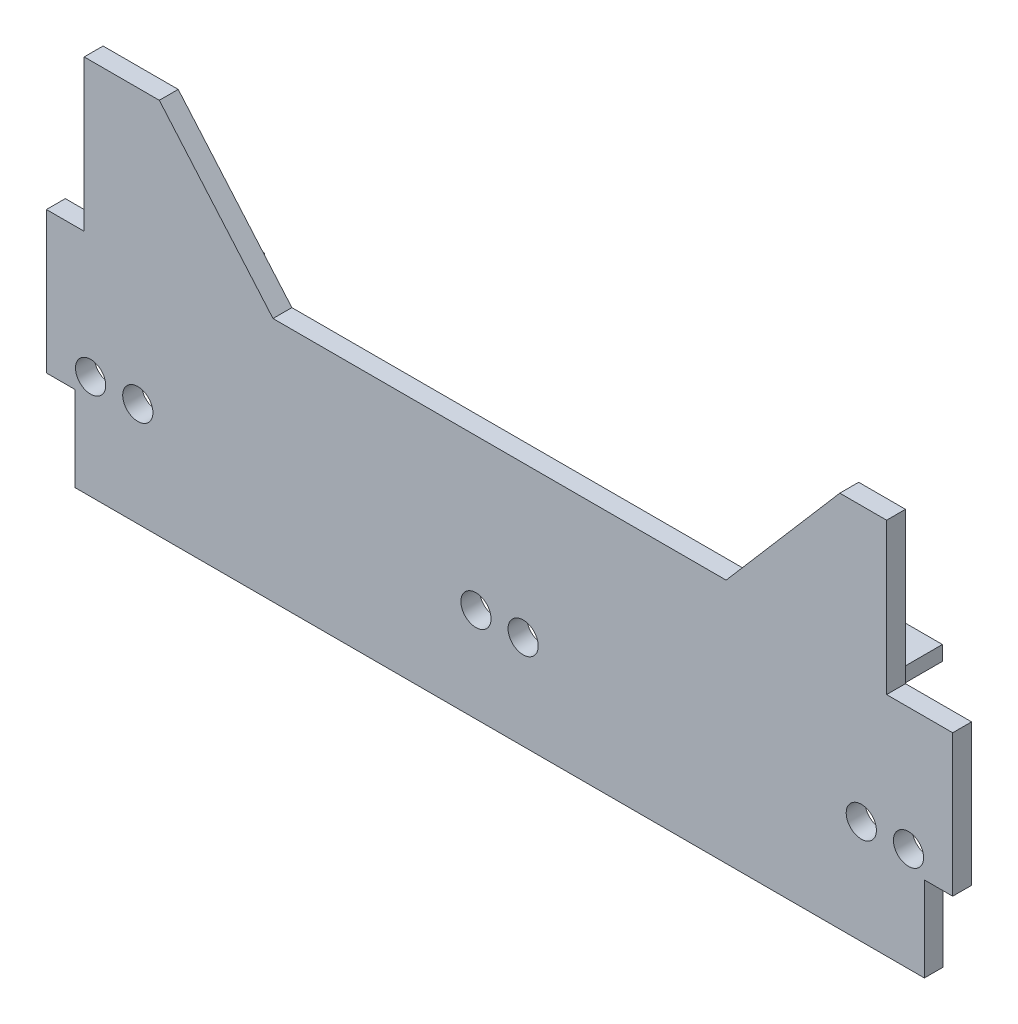
SolidWorks part; units mm, degrees
ref_plane "Front Plane" through (0, 0, 0) normal (0, 0, 1) x (1, 0, 0)
ref_plane "Top Plane" through (0, 0, 0) normal (0, 1, 0) x (1, 0, 0)
ref_plane "Right Plane" through (0, 0, 0) normal (1, 0, 0) x (0, 0, -1)
sketch "Sketch1" plane through (0, 0, 0) normal (0, 0, 1) x (1, 0, 0)
  line L1 (-240, -100) -> (240, -100)
  line L2 (-240, -100) -> (-240, 100)
  line L3 (-240, 100) -> (240, 100)
  line L4 (240, -100) -> (240, 100)
  line L5 (-240, -100) -> (240, 100) construction
  line L6 (-240, 100) -> (240, -100) construction
  point P0 (0, 0)
  dimension "D1" = 480
  dimension "D2" = 200
extrude "Boss-Extrude1" add sketch "Sketch1" along normal blind 10
sketch "Sketch2" plane through (0, 0, 0) normal (0, 0, -1) x (-1, 0, 0)
  line L0 (-240, 0) -> (240, 0) construction
  line L1 (-240, -100) -> (-240, 100) construction
  line L2 (240, 100) -> (240, -100) construction
  line L3 (0, 100) -> (0, -100) construction
  line L4 (-194.555, 17.7614) -> (-164.555, 17.7614)
  line L5 (-194.555, 17.7614) -> (-194.555, 10)
  line L6 (-194.555, 10) -> (-164.555, 10)
  line L7 (-164.555, 17.7614) -> (-164.555, 10)
  line L8 (-240, 100) -> (240, 100) construction
  line L9 (240, -100) -> (-240, -100) construction
  line L10 (164.555, 17.7614) -> (164.555, 10)
  line L11 (194.555, 17.7614) -> (164.555, 17.7614)
  line L12 (194.555, 17.7614) -> (194.555, 10)
  line L13 (194.555, 10) -> (164.555, 10)
  dimension "D1" = 30
  dimension "D2" = 45.445
  dimension "D3" = 10
extrude "Boss-Extrude2" add sketch "Sketch2" along normal blind 30
sketch "Sketch3" plane through (0, 17.7614, 0) normal (0, 1, 0) x (1, 0, 0)
  line L0 (194.555, 15) -> (164.555, 15) construction
  line L1 (194.555, 30) -> (194.555, 0) construction
  line L2 (164.555, 30) -> (164.555, 0) construction
  line L3 (0, 0) -> (0, 161.0964) construction
  circle A0 centre (179.555, 15) radius 5
  circle A1 centre (-179.555, 15) radius 5
  dimension "D1" = 10
extrude "Cut-Extrude1" cut sketch "Sketch3" against normal blind 30
sketch "Sketch5" plane through (0, 0, 10) normal (0, 0, 1) x (1, 0, 0)
  line L0 (-240, -100) -> (240, -100) construction
  line L1 (140, 100) -> (90, 30)
  line L2 (0, 0) -> (0, 100) construction
  line L3 (240, 100) -> (-240, 100) construction
  line L4 (-216.6, -45) -> (-191.6, -45) construction
  line L5 (216.6, -45) -> (191.6, -45) construction
  line L6 (-140, 100) -> (-90, 30)
  line L7 (-140, 30) -> (140, 30) construction
  line L8 (-140, 30) -> (-140, 100) construction
  line L9 (-140, 100) -> (140, 100)
  line L10 (140, 30) -> (140, 100) construction
  line L11 (-140, 30) -> (140, 100) construction
  line L12 (-140, 100) -> (140, 30) construction
  line L13 (-90, 30) -> (90, 30)
  circle A0 centre (-12.5, -50) radius 8
  circle A1 centre (-216.6, -45) radius 8
  circle A2 centre (-191.6, -45) radius 8
  circle A4 centre (12.5, -50) radius 8
  circle A6 centre (191.6, -45) radius 8
  circle A7 centre (216.6, -45) radius 8
  point P3 (0, 65)
  dimension "D1" = 16
  dimension "D3" = 216.6
  dimension "D4" = 16
  dimension "D7" = 70
  dimension "D5" = 50
  dimension "D2" = 12.5
  dimension "D6" = 25
  dimension "D8" = 280
  dimension "D9" = 50
  dimension "D10" = 50
extrude "Cut-Extrude2" cut sketch "Sketch5" against normal blind 30
sketch "Sketch6" plane through (0, 0, 0) normal (0, 0, -1) x (-1, 0, 0)
  line L0 (-240, 100) -> (-140, 100) construction
  line L1 (-240, -100) -> (-225, -100)
  line L2 (-240, -100) -> (-240, -55)
  line L3 (-240, -55) -> (-225, -55)
  line L4 (-225, -100) -> (-225, -55)
  line L5 (240, -100) -> (225, -100)
  line L6 (240, -100) -> (240, -55)
  line L7 (240, -55) -> (225, -55)
  line L8 (225, -100) -> (225, -55)
  line L9 (240, 20) -> (220, 20)
  line L10 (240, 20) -> (240, 100)
  line L11 (240, 100) -> (220, 100)
  line L12 (220, 20) -> (220, 100)
  line L13 (-240, 20) -> (-205, 20)
  line L14 (-240, 20) -> (-240, 100)
  line L15 (-240, 100) -> (-205, 100)
  line L16 (-205, 20) -> (-205, 100)
  line L17 (240, 100) -> (240, -100) construction
  line L18 (140, 100) -> (240, 100) construction
  line L19 (90, 30) -> (140.207, 100) construction
  line L20 (-90, 30) -> (90, 30) construction
  line L21 (140, 100) -> (240, 100) construction
  line L22 (140.207, 100) -> (180.207, 100)
  line L23 (-120, 30) -> (-90, 30)
  line L24 (0, 0) -> (0, 106.1435) construction
  line L25 (-180.207, 100) -> (-120, 30)
  line L26 (-140.207, 100) -> (-180.207, 100)
  line L27 (-90, 30) -> (-140.207, 100) construction
  line L28 (140.207, 100) -> (114.97, 100)
  line L29 (114.97, 100) -> (90, 30)
  line L30 (-140.207, 100) -> (-114.97, 100)
  line L31 (-114.97, 100) -> (-90, 30)
  line L32 (180.207, 100) -> (120, 30)
  line L33 (120, 30) -> (90, 30)
  point P22 (240, 0)
  dimension "D1" = 45
  dimension "D2" = 45
  dimension "D3" = 15
  dimension "D4" = 15
  dimension "D5" = 20
  dimension "D6" = 35
  dimension "D7" = 80
  dimension "D8" = 80
  dimension "D9" = 40
  dimension "D10" = 30
extrude "Cut-Extrude3" cut sketch "Sketch6" against normal blind 10
equation "\"1y\"=11.3883"
